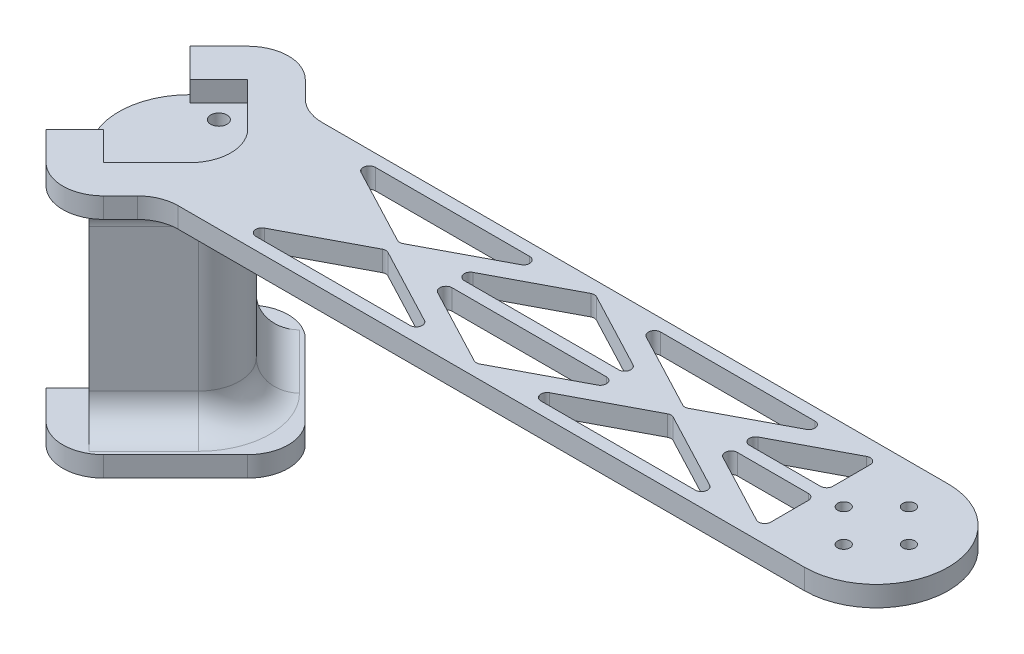
SolidWorks part; units mm, degrees
ref_plane "Front Plane" through (0, 0, 0) normal (0, 0, 1) x (1, 0, 0)
ref_plane "Top Plane" through (0, 0, 0) normal (0, 1, 0) x (1, 0, 0)
ref_plane "Right Plane" through (0, 0, 0) normal (1, 0, 0) x (0, 0, -1)
sketch "Sketch1" plane through (0, 0, 0) normal (0, 1, 0) x (1, 0, 0)
  line L0 (-7.0711, -7.0711) -> (-17.6777, -17.6777)
  line L1 (-7.0711, 7.0711) -> (-17.6777, 17.6777)
  line L2 (-17.6777, -17.6777) -> (-24.7487, -10.6066)
  line L3 (-17.6777, 17.6777) -> (-24.7487, 10.6066)
  line L4 (-24.7487, -10.6066) -> (-17.6777, -17.6777)
  line L5 (-24.7487, -10.6066) -> (-31.8198, -17.6777)
  line L6 (-24.7487, 10.6066) -> (-31.8198, 17.6777)
  line L7 (-31.8198, 17.6777) -> (-24.7487, 24.7487)
  line L8 (-31.8198, -17.6777) -> (-24.7487, -24.7487)
  line L9 (-1017.6777, 17.6777) -> (48982.3223, 17.6777) construction
  line L10 (-1017.6777, -17.6777) -> (48982.3223, -17.6777) construction
  line L11 (-10.6066, -24.7487) -> (-6.4645, -20.6066)
  line L12 (-10.6066, 24.7487) -> (-6.4645, 20.6066)
  line L13 (0, 0) -> (154.3, 0) construction
  line L14 (0.6066, 17.6777) -> (154.3, 17.6777)
  line L15 (0.6066, -17.6777) -> (154.3, -17.6777)
  line L16 (0.6066, 17.6777) -> (0.6066, -17.6777) construction
  line L17 (154.3, 17.6777) -> (154.3, -17.6777) construction
  line L18 (144.8, -17.6777) -> (144.8, 17.6777) construction
  line L19 (0.6066, 17.6777) -> (0.6066, 14.6777) construction
  line L20 (0.6066, 0) -> (0.6066, 1.5) construction
  line L21 (-999.3934, 14.6777) -> (49000.6066, 14.6777) construction
  line L22 (-999.3934, 1.5) -> (49000.6066, 1.5) construction
  line L26 (0.6066, 14.6777) -> (10.6066, 14.6777) construction
  line L27 (25.6066, 1.5) -> (35.6066, 1.5) construction
  line L28 (10.6066, 14.6777) -> (60.6066, 14.6777) construction
  line L29 (35.6066, 1.5) -> (45.6066, 1.5) construction
  line L30 (45.6066, 1.5) -> (95.6066, 1.5) construction
  line L31 (60.6066, 14.6777) -> (70.6066, 14.6777) construction
  line L32 (95.6066, 1.5) -> (105.6066, 1.5) construction
  line L33 (15.9697, 11.8507) -> (34.9072, 1.8687)
  line L34 (36.306, 1.8687) -> (55.2435, 11.8507)
  line L35 (54.544, 14.6777) -> (16.6692, 14.6777)
  line L36 (50.9697, 4.3269) -> (69.9072, 14.309)
  line L37 (71.306, 14.309) -> (90.2435, 4.3269)
  line L38 (89.544, 1.5) -> (51.6692, 1.5)
  line L39 (70.6066, 14.6777) -> (80.6066, 14.6777)
  line L40 (105.6066, 1.5) -> (115.6066, 1.5) construction
  line L41 (80.6066, 14.6777) -> (130.6066, 14.6777) construction
  line L42 (130.6066, 14.6777) -> (140.6066, 14.6777) construction
  line L43 (85.9697, 11.8507) -> (104.9072, 1.8687)
  line L44 (106.306, 1.8687) -> (125.2435, 11.8507)
  line L45 (124.544, 14.6777) -> (86.6692, 14.6777)
  line L46 (120.9697, 4.3269) -> (138.4072, 13.5183)
  line L47 (140.6066, 12.1914) -> (140.6066, 3)
  line L48 (139.1066, 1.5) -> (121.6692, 1.5)
  line L49 (140.6066, -12.1914) -> (140.6066, -3)
  line L50 (120.9697, -4.3269) -> (138.4072, -13.5183)
  line L51 (139.1066, -1.5) -> (121.6692, -1.5)
  line L52 (124.544, -14.6777) -> (86.6692, -14.6777)
  line L53 (106.306, -1.8687) -> (125.2435, -11.8507)
  line L54 (85.9697, -11.8507) -> (104.9072, -1.8687)
  line L55 (71.306, -14.309) -> (90.2435, -4.3269)
  line L56 (50.9697, -4.3269) -> (69.9072, -14.309)
  line L57 (89.544, -1.5) -> (51.6692, -1.5)
  line L58 (36.306, -1.8687) -> (55.2435, -11.8507)
  line L59 (15.9697, -11.8507) -> (34.9072, -1.8687)
  line L60 (54.544, -14.6777) -> (16.6692, -14.6777)
  circle A0 centre (154.3, 0) radius 8 construction
  arc A1 (154.3, 17.6777) -> (154.3, -17.6777) centre (154.3, 0) cw
  circle A2 centre (146.3, 0) radius 1.5
  circle A3 centre (154.3, -8) radius 1.5
  circle A4 centre (162.3, 0) radius 1.5
  circle A5 centre (154.3, 8) radius 1.5
  arc A6 (-6.4645, 20.6066) -> (0.6066, 17.6777) centre (0.6066, 27.6777) ccw
  arc A7 (-6.4645, -20.6066) -> (0.6066, -17.6777) centre (0.6066, -27.6777) cw
  arc A8 (-24.7487, -24.7487) -> (-10.6066, -24.7487) centre (-17.6777, -17.6777) ccw
  arc A9 (-24.7487, 24.7487) -> (-10.6066, 24.7487) centre (-17.6777, 17.6777) cw
  arc A10 (140.6066, 3) -> (139.1066, 1.5) centre (139.1066, 3) cw
  arc A11 (138.4072, 13.5183) -> (140.6066, 12.1914) centre (139.1066, 12.1914) cw
  arc A12 (120.9697, 4.3269) -> (121.6692, 1.5) centre (121.6692, 3) ccw
  arc A13 (125.2435, 11.8507) -> (124.544, 14.6777) centre (124.544, 13.1777) ccw
  arc A14 (104.9072, 1.8687) -> (106.306, 1.8687) centre (105.6066, 3.1956) ccw
  arc A15 (86.6692, 14.6777) -> (85.9697, 11.8507) centre (86.6692, 13.1777) ccw
  arc A16 (90.2435, 4.3269) -> (89.544, 1.5) centre (89.544, 3) cw
  arc A17 (71.306, 14.309) -> (69.9072, 14.309) centre (70.6066, 12.982) ccw
  arc A18 (50.9697, 4.3269) -> (51.6692, 1.5) centre (51.6692, 3) ccw
  arc A19 (55.2435, 11.8507) -> (54.544, 14.6777) centre (54.544, 13.1777) ccw
  arc A20 (15.9697, 11.8507) -> (16.6692, 14.6777) centre (16.6692, 13.1777) cw
  arc A21 (34.9072, 1.8687) -> (36.306, 1.8687) centre (35.6066, 3.1956) ccw
  arc A25 (138.4072, -13.5183) -> (140.6066, -12.1914) centre (139.1066, -12.1914) ccw
  arc A26 (140.6066, -3) -> (139.1066, -1.5) centre (139.1066, -3) ccw
  arc A27 (120.9697, -4.3269) -> (121.6692, -1.5) centre (121.6692, -3) cw
  arc A28 (125.2435, -11.8507) -> (124.544, -14.6777) centre (124.544, -13.1777) cw
  arc A29 (104.9072, -1.8687) -> (106.306, -1.8687) centre (105.6066, -3.1956) cw
  arc A30 (86.6692, -14.6777) -> (85.9697, -11.8507) centre (86.6692, -13.1777) cw
  arc A31 (71.306, -14.309) -> (69.9072, -14.309) centre (70.6066, -12.982) cw
  arc A32 (90.2435, -4.3269) -> (89.544, -1.5) centre (89.544, -3) ccw
  arc A33 (50.9697, -4.3269) -> (51.6692, -1.5) centre (51.6692, -3) cw
  arc A34 (34.9072, -1.8687) -> (36.306, -1.8687) centre (35.6066, -3.1956) cw
  arc A35 (55.2435, -11.8507) -> (54.544, -14.6777) centre (54.544, -13.1777) cw
  arc A36 (15.9697, -11.8507) -> (16.6692, -14.6777) centre (16.6692, -13.1777) ccw
  arc A40 (-7.0711, -7.0711) -> (-7.0711, 7.0711) centre (-14.1421, 0) ccw
  point P25 (154.3, 0)
  point P26 (-3.5355, 17.6777)
  point P33 (154.3, 0)
  point P36 (-3.5355, -17.6777)
  point P44 (144.8, 0)
  point P68 (140.6066, 1.5)
  dimension "D2" = 4
  dimension "D3" = 10
  dimension "D6" = 1.5
  dimension "D7" = 10
  dimension "D1" = 35.3553
  dimension "D4" = 153.6934
  dimension "D5" = 144.1934
extrude "Boss-Extrude1" add sketch "Sketch1" along normal blind 5
sketch "Sketch2" plane through (0, 0, 0) normal (0, -1, 0) x (1, 0, 0)
  line L0 (-24.7487, 10.6066) -> (-24.7487, -10.6066)
  line L1 (-24.7487, -10.6066) -> (-17.6777, -17.6777)
  line L2 (-17.6777, -17.6777) -> (0, 0)
  line L3 (0, 0) -> (-17.6777, 17.6777)
  line L4 (-24.7487, 10.6066) -> (-21.2132, 14.1421)
  line L5 (-17.6777, 17.6777) -> (-24.7487, 10.6066) construction
  line L6 (-24.7487, -10.6066) -> (-21.2132, -14.1421)
  line L7 (-21.2132, 14.1421) -> (-17.6777, 10.6066) construction
  line L8 (-21.2132, -14.1421) -> (-17.6777, -10.6066) construction
  line L9 (-24.7487, 10.6066) -> (-24.7487, -10.6066)
  line L10 (-17.6777, -17.6777) -> (0, 0)
  line L11 (-17.6777, 17.6777) -> (-24.7487, 10.6066)
  line L12 (-17.6777, -17.6777) -> (-19.4454, -19.4454) construction
  line L13 (-17.6777, 17.6777) -> (-19.4454, 19.4454) construction
  line L18 (-24.7487, -1000) -> (-24.7487, 49000) construction
  line L19 (-19.4454, 19.4454) -> (-17.6777, 17.6777) construction
  line L20 (-19.4454, 19.4454) -> (-18.3848, 20.5061) construction
  line L21 (-19.4454, -19.4454) -> (-18.3848, -20.5061) construction
  line L22 (-725.4916, -727.6129) -> (34629.8475, 34627.7262) construction
  line L23 (-725.4916, 727.6129) -> (34629.8475, -34627.7262) construction
  line L24 (-18.3848, 20.5061) -> (2.1213, 0)
  line L25 (-18.3848, 20.5061) -> (-26.5165, 12.3744)
  line L26 (2.1213, 0) -> (-18.3848, -20.5061)
  line L27 (-26.5165, -12.3744) -> (-18.3848, -20.5061)
  circle A0 centre (-17.6777, 10.6066) radius 2
  circle A1 centre (-17.6777, -10.6066) radius 2
  arc A3 (-26.5165, 12.3744) -> (-26.5165, -12.3744) centre (-14.1421, 0) ccw
  point P0 (-24.7487, 10.6066)
  point P1 (-24.7487, -10.6066)
  point P3 (-17.6777, -17.6777)
  point P5 (0, 0)
  point P7 (-17.6777, 17.6777)
  point P26 (-24.7487, 14.1421)
  point P29 (-24.7487, 0)
  point P30 (-24.7487, -14.1421)
  dimension "D1" = 17.5
extrude "Boss-Extrude13" add sketch "Sketch2" along normal blind 50 contours L3 L11 L4 L0 L1 L2 A1 A0 | L25 A3 L27 L26 L24 L11 L3 L2 L1 L0 L4
fillet "Fillet3" radius 10 1 edges at (2.1213, -25, 0)
fillet "Fillet8" radius 7.5 3 edges at (-11.6673, 0, 13.7886) (-2.0208, 0, 0) (-11.6673, 0, -13.7886)
sketch "Sketch3" plane through (0, -50, 0) normal (0, -1, 0) x (1, 0, 0)
  line L0 (-7.0711, -7.0711) -> (-17.6777, -17.6777)
  line L1 (-7.0711, 7.0711) -> (-17.6777, 17.6777)
  line L2 (-17.6777, 17.6777) -> (-24.7487, 10.6066)
  line L3 (-17.6777, -17.6777) -> (-24.7487, -10.6066)
  line L4 (-24.7487, 10.6066) -> (-31.8198, 17.6777)
  line L5 (-26.5165, 12.3744) -> (-31.8198, 17.6777) construction
  line L6 (-24.7487, -10.6066) -> (-31.8198, -17.6777)
  line L7 (-26.5165, -12.3744) -> (-31.8198, -17.6777) construction
  line L8 (-31.8198, 17.6777) -> (-24.7487, 24.7487)
  line L9 (-31.8198, -17.6777) -> (-24.7603, -24.7372)
  line L10 (-1000, 0) -> (49000, 0) construction
  line L11 (-10.6182, -24.7372) -> (7.0595, -7.0595)
  line L12 (-10.6066, 24.7487) -> (7.0595, 7.0827)
  arc A0 (-24.7603, -24.7372) -> (-10.6182, -24.7372) centre (-17.6893, -17.6661) ccw
  arc A1 (-24.7487, 24.7487) -> (-10.6066, 24.7487) centre (-17.6777, 17.6777) cw
  arc A2 (7.0595, 7.0827) -> (7.0595, -7.0595) centre (-0.0116, 0.0116) cw
  arc A3 (-7.0711, -7.0711) -> (-7.0711, 7.0711) centre (-14.1421, 0) ccw
  point P25 (0, 0)
  dimension "D1" = 10
  dimension "D2" = 10
  dimension "D3" = 10
extrude "Boss-Extrude14" add sketch "Sketch3" along normal blind 5 contours A2 L11 A0 L9 L6 L3 L0 A3 L1 L2 L4 L8 A1 L12
fillet "Fillet9" radius 7.5 3 edges at (-11.6673, -50, -13.7886) (-2.0208, -50, 0) (-11.6673, -50, 13.7886)
